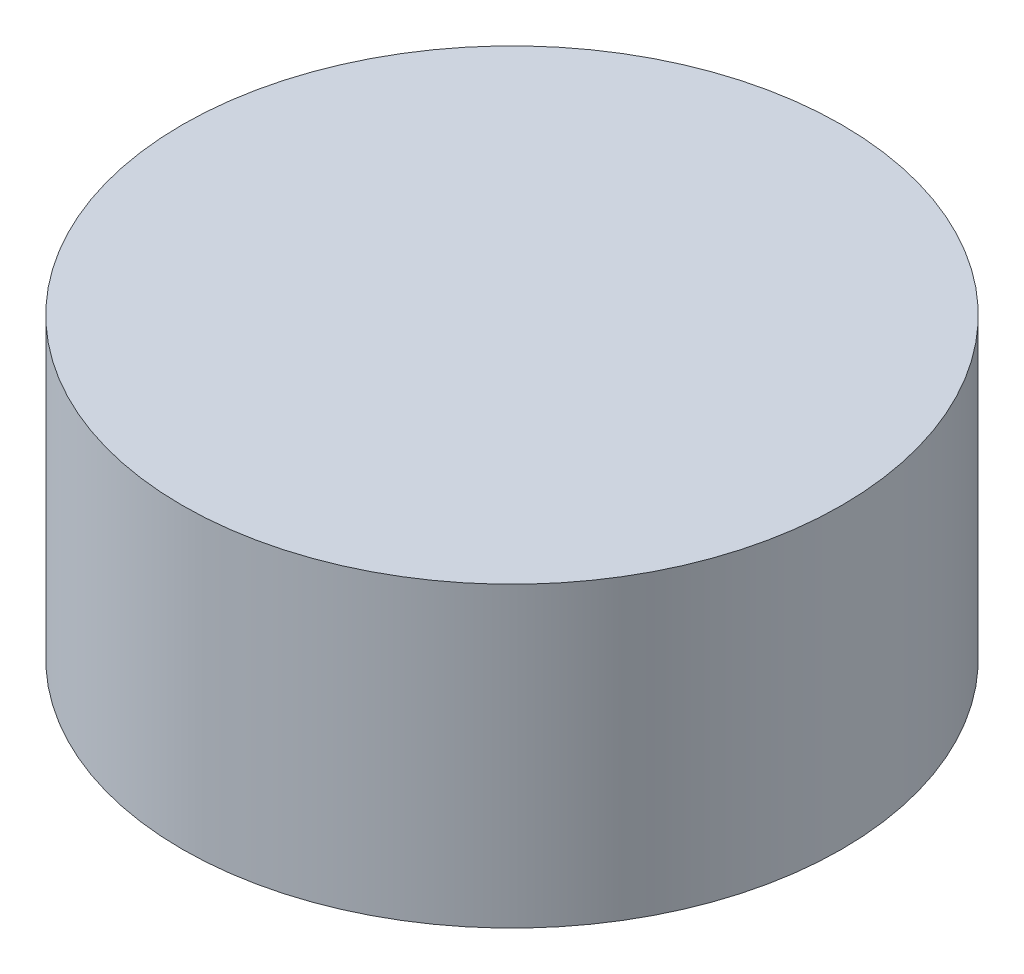
SolidWorks part; units mm, degrees
material "PA Tipo 6"
ref_plane "Plano frontal" through (0, 0, 0) normal (0, 0, 1) x (1, 0, 0)
ref_plane "Plano superior" through (0, 0, 0) normal (0, 1, 0) x (1, 0, 0)
ref_plane "Plano direito" through (0, 0, 0) normal (1, 0, 0) x (0, 0, -1)
sketch "Esboço1" plane through (0, 0, 0) normal (0, 1, 0) x (1, 0, 0)
  circle A0 centre (0, 0) radius 7.75
  point P2 (0, 0)
  dimension "D1" = 15.5
extrude "Ressalto-extrusão1" add sketch "Esboço1" along normal blind 7
